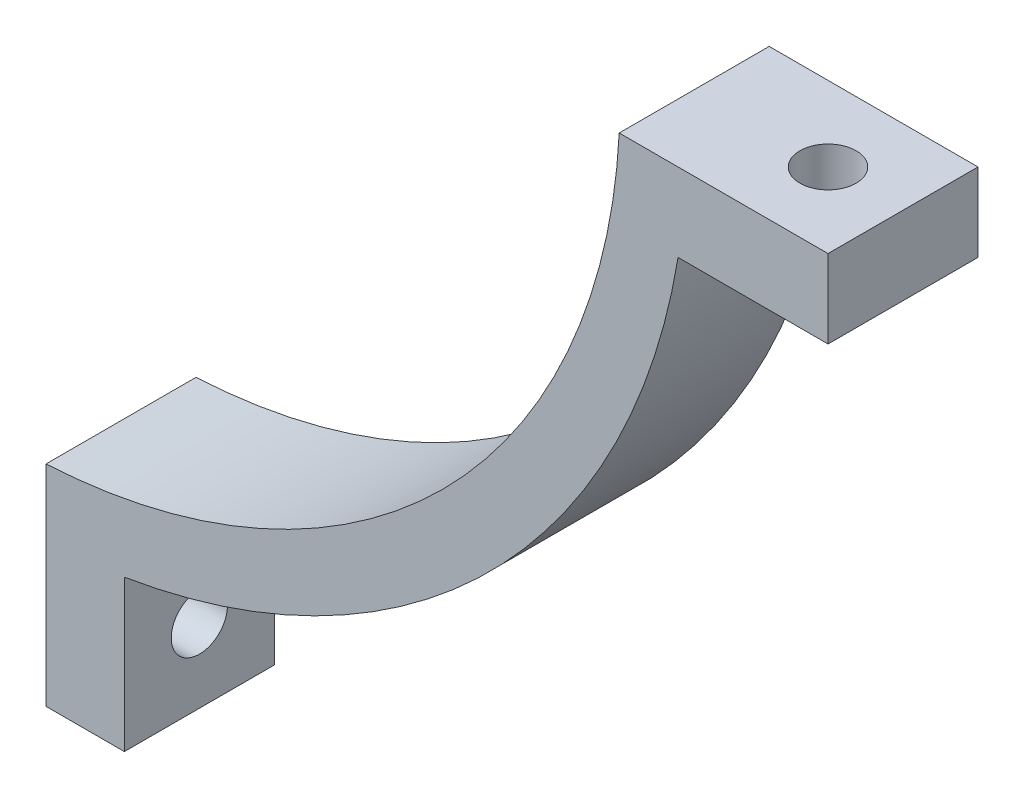
SolidWorks part; units mm, degrees
ref_plane "Front Plane" through (0, 0, 0) normal (0, 0, 1) x (1, 0, 0)
ref_plane "Top Plane" through (0, 0, 0) normal (0, 1, 0) x (1, 0, 0)
ref_plane "Right Plane" through (0, 0, 0) normal (1, 0, 0) x (0, 0, -1)
sketch "Sketch1" plane through (0, 0, 0) normal (0, 0, 1) x (1, 0, 0)
  line L0 (-230.5002, 0) -> (230.5002, 0) construction
  line L1 (0, 230.5002) -> (0, -230.5002) construction
  line L2 (230.5002, -2.3812) -> (230.5002, 2.3813) construction
  line L3 (230.5002, 2.3813) -> (50.9222, 2.3813) construction
  line L4 (-230.5002, -2.3812) -> (-230.5002, 2.3812) construction
  line L5 (230.5002, -2.3812) -> (50.9222, -2.3812) construction
  line L6 (-230.5002, 2.3812) -> (-50.9222, 2.3812) construction
  line L7 (-230.5002, -2.3812) -> (-50.9222, -2.3813) construction
  line L8 (-2.3813, -230.5002) -> (2.3812, -230.5002) construction
  line L9 (2.3812, -230.5002) -> (2.3812, -50.9222) construction
  line L10 (-2.3813, -230.5002) -> (-2.3812, -50.9222) construction
  line L11 (-2.3813, 230.5002) -> (-2.3812, 50.9222) construction
  line L12 (-2.3813, 230.5002) -> (2.3812, 230.5002) construction
  line L13 (2.3812, 230.5002) -> (2.3812, 50.9222) construction
  line L14 (51.1762, -2.6353) -> (68.8595, -2.6353)
  line L15 (68.8595, -2.6353) -> (68.8595, -9.271)
  line L16 (2.6352, -51.1762) -> (2.6352, -68.9562)
  line L17 (2.6352, -68.9562) -> (9.271, -68.9562)
  line L18 (9.271, -68.9562) -> (9.271, -56.1595)
  line L19 (68.8595, -9.271) -> (56.1595, -9.271)
  circle A0 centre (0, 0) radius 50.9778 construction
  arc A1 (51.1762, -2.6353) -> (2.6352, -51.1762) centre (0, 0) cw
  arc A2 (56.1595, -9.271) -> (9.271, -56.1595) centre (0, 0) cw
  point P6 (0, 0)
  point P9 (0, 0)
  point P10 (0, 0)
  point P18 (-230.5002, 0)
  point P20 (0, -230.5002)
  dimension "D3" = 101.9556
  dimension "D4" = 4.7625
  dimension "D5" = 179.578
  dimension "D1" = 0.254
  dimension "D2" = 0.254
  dimension "D6" = 0.254
  dimension "D7" = 4.7625
  dimension "D8" = 179.578
  dimension "D9" = 179.578
extrude "Boss-Extrude3" add sketch "Sketch1" along normal blind 12.7
sketch "Sketch2" plane through (9.271, 0, 0) normal (1, 0, 0) x (0, 0, -1)
  line L0 (-12.7, -68.9562) -> (-12.7, -56.1595) construction
  line L1 (-12.7, -68.9562) -> (0, -68.9562) construction
  circle A0 centre (-6.35, -62.6062) radius 2.3812
  dimension "D1" = 4.7625
  dimension "D2" = 6.35
  dimension "D3" = 6.35
extrude "Cut-Extrude1" cut sketch "Sketch2" against normal through all
sketch "Sketch3" plane through (0, -9.271, 0) normal (0, -1, 0) x (1, 0, 0)
  line L0 (68.8595, 12.7) -> (68.8595, 0) construction
  line L1 (56.1595, 12.7) -> (68.8595, 12.7) construction
  circle A0 centre (62.5095, 6.35) radius 2.3813
  dimension "D1" = 6.35
  dimension "D3" = 4.7625
  dimension "D2" = 6.35
extrude "Cut-Extrude2" cut sketch "Sketch3" against normal through all
equation "\"Fin Thickness\" = 3 / 16"
equation "\"D4@Sketch1\"=\"Fin Thickness\""
equation "\"Fin Length\"= 7.07in"
equation "\"D5@Sketch1\"=\"Fin Length\""
equation "\"Outer Diameter\"= 4.014in"
equation "\"D3@Sketch1\"=\"Outer Diameter\""
equation "\"D7@Sketch1\"=\"Fin Thickness\""
equation "\"D8@Sketch1\"=\"Fin Length\""
equation "\"D9@Sketch1\"=\"Fin Length\""
